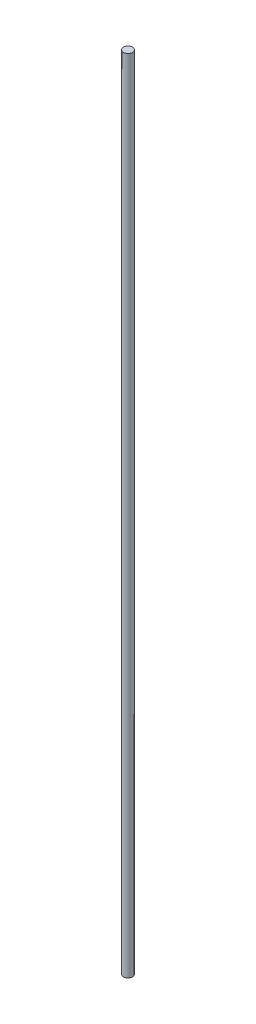
SolidWorks part; units mm, degrees
ref_plane "Front Plane" through (0, 0, 0) normal (0, 0, 1) x (1, 0, 0)
ref_plane "Top Plane" through (0, 0, 0) normal (0, 1, 0) x (1, 0, 0)
ref_plane "Right Plane" through (0, 0, 0) normal (1, 0, 0) x (0, 0, -1)
sketch "Sketch1" plane through (0, 0, 0) normal (0, 0, 1) x (1, 0, 0)
  line L0 (4, 700) -> (0, 700)
  line L1 (0, 700) -> (0, 0)
  line L2 (0, 0) -> (4, 0)
  line L3 (4, 0) -> (4, 700)
  line L4 (0, 700) -> (0, 0) construction
  dimension "D1" = 4
  dimension "D2" = 700
revolve "Revolve1" add sketch "Sketch1" angle 360 about L4
